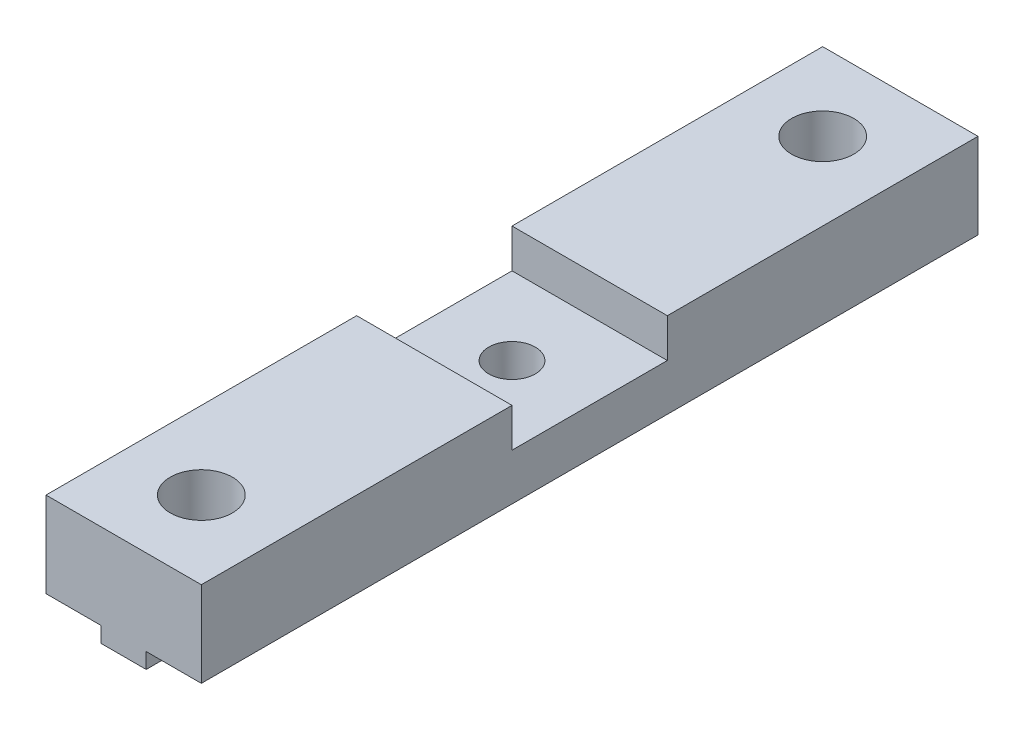
SolidWorks part; units mm, degrees
ref_plane "Front Plane" through (0, 0, 0) normal (0, 0, 1) x (1, 0, 0)
ref_plane "Top Plane" through (0, 0, 0) normal (0, 1, 0) x (1, 0, 0)
ref_plane "Right Plane" through (0, 0, 0) normal (1, 0, 0) x (0, 0, -1)
sketch "Sketch1" plane through (0, 0, 0) normal (0, 0, 1) x (1, 0, 0)
  line L0 (-5, 0) -> (5, 0)
  line L1 (5, 0) -> (5, -5.5)
  line L2 (5, -5.5) -> (1.45, -5.5)
  line L3 (1.45, -5.5) -> (1.45, -6.5)
  line L4 (1.45, -6.5) -> (-1.45, -6.5)
  line L5 (-1.45, -6.5) -> (-1.45, -5.5)
  line L6 (-1.45, -5.5) -> (-5, -5.5)
  line L7 (-5, -5.5) -> (-5, 0)
  point P6 (0, -6.5)
  point P9 (0, 0)
  point P11 (0, 3.0391)
  dimension "D1" = 10
  dimension "D2" = 2.9
  dimension "D3" = 5.5
  dimension "D4" = 1
extrude "Main" add sketch "Sketch1" along normal mid plane 50
sketch "Sketch2" plane through (0, 0, 0) normal (0, 1, 0) x (1, 0, 0)
  circle A0 centre (0, 20) radius 2
  circle A1 centre (0, -20) radius 2
  circle A2 centre (0, 0) radius 1.5
  dimension "D2" = 4
  dimension "D4" = 3
  dimension "D1" = 20
  dimension "D3" = 20
extrude "Holes" cut sketch "Sketch2" against normal through all
sketch "Sketch3" plane through (-5, 0, 0) normal (-1, 0, 0) x (0, 0, 1)
  line L0 (25, 0) -> (-25, 0) construction
  line L1 (-5, 0) -> (5, 0)
  line L2 (-5, 0) -> (-5, -2.5)
  line L3 (-5, -2.5) -> (5, -2.5)
  line L4 (5, 0) -> (5, -2.5)
  line L5 (25, -5.5) -> (-25, -5.5) construction
  point P8 (0, -2.5)
  point P9 (0, 0)
  dimension "D1" = 10
  dimension "D2" = 3
extrude "Cut-Extrude2" cut sketch "Sketch3" against normal through all
